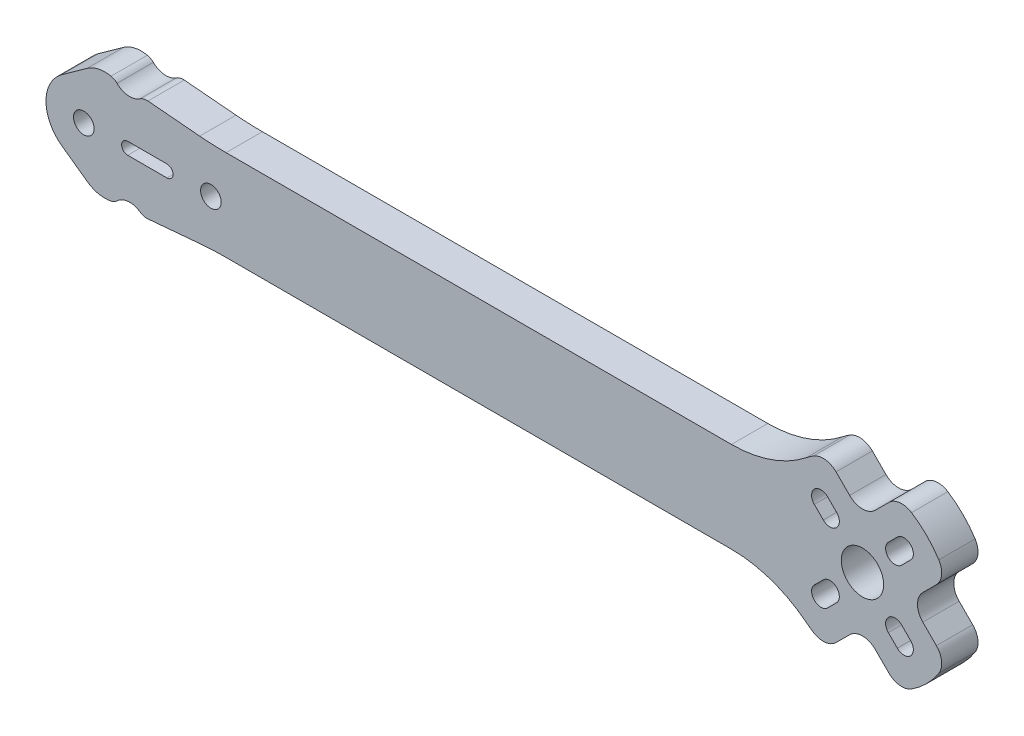
SolidWorks part; units mm, degrees
material "Thornel Mat VMA"
ref_plane "Front Plane" through (0, 0, 0) normal (0, 0, 1) x (1, 0, 0)
ref_plane "Top Plane" through (0, 0, 0) normal (0, 1, 0) x (1, 0, 0)
ref_plane "Right Plane" through (0, 0, 0) normal (1, 0, 0) x (0, 0, -1)
sketch "Sketch1" plane through (0, 0, 0) normal (0, 0, 1) x (1, 0, 0)
  line L0 (6.8589, 6.8589) -> (5.374, 5.374) construction
  line L2 (7.955, 5.7629) -> (6.47, 4.278)
  line L3 (5.7629, 7.955) -> (4.278, 6.47)
  line L4 (-6.8589, 6.8589) -> (-5.374, 5.374) construction
  line L5 (-5.7629, 7.955) -> (-4.278, 6.47)
  line L6 (-7.955, 5.7629) -> (-6.47, 4.278)
  line L7 (5.374, -5.374) -> (-5.374, 5.374) construction
  line L8 (6.8589, -6.8589) -> (5.374, -5.374) construction
  line L9 (5.7629, -7.955) -> (4.278, -6.47)
  line L11 (7.955, -5.7629) -> (6.47, -4.278)
  line L12 (-6.8589, -6.8589) -> (-5.374, -5.374) construction
  line L13 (-7.955, -5.7629) -> (-6.47, -4.278)
  line L14 (-5.7629, -7.955) -> (-4.278, -6.47)
  line L15 (-118.078, -8.4386) -> (-109.5245, -7.6903)
  line L16 (-105.1667, -7.5) -> (-21.6506, -7.5)
  line L17 (-4.367, -12.2159) -> (-2.1213, -9.9702)
  line L18 (2.1213, -9.9702) -> (4.367, -12.2159)
  line L19 (12.2159, -4.367) -> (9.9702, -2.1213)
  line L20 (9.9702, 2.1213) -> (12.2159, 4.367)
  line L21 (4.367, 12.2159) -> (2.1213, 9.9702)
  line L22 (-2.1213, 9.9702) -> (-4.367, 12.2159)
  line L23 (-21.6506, 7.5) -> (-105.1667, 7.5)
  line L24 (-109.5245, 7.6903) -> (-118.078, 8.4386)
  line L25 (-128.1078, 8.1033) -> (-132.3227, 5.0768)
  line L26 (-132.3227, -5.0768) -> (-128.1078, -8.1033)
  line L27 (-121.4272, 1) -> (-114.9272, 1)
  line L28 (-114.9272, -1) -> (-121.4272, -1)
  line L29 (0, 0) -> (-2.4749, 0) construction
  line L30 (-2.4749, 0) -> (-2.4749, 2.4749) construction
  circle A1 centre (0, 0) radius 3.5
  arc A20 (-124.1818, -8.9388) -> (-123.1893, -8.4119) centre (-124.5857, -6.98) ccw
  arc A21 (-119.3893, -8.0916) -> (-123.1893, -8.4119) centre (-121.0948, -10.5597) ccw
  arc A22 (-119.3893, -8.0916) -> (-118.078, -8.4386) centre (-118.2523, -6.4462) ccw
  arc A23 (-105.1667, -7.5) -> (-109.5245, -7.6903) centre (-105.1667, -57.5) ccw
  arc A24 (-9.2788, -11.7857) -> (-21.6506, -7.5) centre (-21.6506, -27.5) ccw
  arc A25 (-9.2788, -11.7857) -> (-8.1105, -12.6183) centre (0, 0) ccw
  arc A26 (-8.1105, -12.6183) -> (-4.367, -12.2159) centre (-6.4884, -10.0946) ccw
  arc A27 (2.1213, -9.9702) -> (-2.1213, -9.9702) centre (0, -12.0915) ccw
  arc A28 (4.367, -12.2159) -> (8.1105, -12.6183) centre (6.4884, -10.0946) ccw
  arc A29 (8.1105, -12.6183) -> (12.6183, -8.1105) centre (0, 0) ccw
  arc A30 (12.6183, -8.1105) -> (12.2159, -4.367) centre (10.0946, -6.4884) ccw
  arc A31 (9.9702, 2.1213) -> (9.9702, -2.1213) centre (12.0915, 0) ccw
  arc A32 (12.2159, 4.367) -> (12.6183, 8.1105) centre (10.0946, 6.4884) ccw
  arc A33 (12.6183, 8.1105) -> (8.1105, 12.6183) centre (0, 0) ccw
  arc A34 (8.1105, 12.6183) -> (4.367, 12.2159) centre (6.4884, 10.0946) ccw
  arc A35 (-2.1213, 9.9702) -> (2.1213, 9.9702) centre (0, 12.0915) ccw
  arc A36 (-4.367, 12.2159) -> (-8.1105, 12.6183) centre (-6.4884, 10.0946) ccw
  arc A37 (-8.1105, 12.6183) -> (-9.2788, 11.7857) centre (0, 0) ccw
  arc A38 (-21.6506, 7.5) -> (-9.2788, 11.7857) centre (-21.6506, 27.5) ccw
  arc A39 (-109.5245, 7.6903) -> (-105.1667, 7.5) centre (-105.1667, 57.5) ccw
  arc A40 (-118.078, 8.4386) -> (-119.3893, 8.0916) centre (-118.2523, 6.4462) ccw
  arc A41 (-123.1893, 8.4119) -> (-119.3893, 8.0916) centre (-121.0948, 10.5597) ccw
  arc A42 (-123.1893, 8.4119) -> (-124.1818, 8.9388) centre (-124.5857, 6.98) ccw
  arc A43 (-124.1818, 8.9388) -> (-128.1078, 8.1033) centre (-125.1915, 4.0418) ccw
  arc A44 (-132.3227, 5.0768) -> (-132.3227, -5.0768) centre (-128.6772, 0) ccw
  arc A45 (-128.1078, -8.1033) -> (-124.1818, -8.9388) centre (-125.1915, -4.0418) ccw
  arc A46 (-121.4272, 1) -> (-121.4272, -1) centre (-121.4272, 0) ccw
  arc A47 (-114.9272, -1) -> (-114.9272, 1) centre (-114.9272, 0) ccw
  arc A48 (-5.7629, 7.955) -> (-7.955, 5.7629) centre (-6.8589, 6.8589) ccw
  arc A49 (-6.47, 4.278) -> (-4.278, 6.47) centre (-5.374, 5.374) ccw
  arc A50 (7.955, 5.7629) -> (5.7629, 7.955) centre (6.8589, 6.8589) ccw
  arc A51 (4.278, 6.47) -> (6.47, 4.278) centre (5.374, 5.374) ccw
  arc A52 (5.7629, -7.955) -> (7.955, -5.7629) centre (6.8589, -6.8589) ccw
  arc A53 (6.47, -4.278) -> (4.278, -6.47) centre (5.374, -5.374) ccw
  arc A54 (-7.955, -5.7629) -> (-5.7629, -7.955) centre (-6.8589, -6.8589) ccw
  arc A55 (-4.278, -6.47) -> (-6.47, -4.278) centre (-5.374, -5.374) ccw
  point P12 (6.1165, 6.1165)
  point P21 (-6.1165, 6.1165)
  point P26 (6.1165, -6.1165)
  point P29 (0, 0)
  point P102 (-6.1165, -6.1165)
  point P107 (0, 0)
  dimension "D1" = 7
  dimension "D2" = 3.1
  dimension "D3" = 2.1
  dimension "D4" = 15.2
  dimension "D5" = 4
extrude "Boss-Extrude1" add sketch "Sketch1" along normal blind 6
hole_wizard "M3 Clearance Hole1" positions "Sketch2" profile "Sketch3" hole size "M3" standard "ANSI Metric" end condition up to next
sketch "Sketch2" plane through (0, 0, 6) normal (0, 0, 1) x (1, 0, 0)
  line L0 (-128.6772, 0) -> (-107.6772, 0) construction
  arc A0 (-132.3227, 5.0768) -> (-132.3227, -5.0768) centre (-128.6772, 0) ccw construction
  point P0 (-107.6772, 0)
  point P3 (-128.6772, 0)
  dimension "D1" = 21
sketch "Sketch3" plane through (-107.6772, 0, 6) normal (1, 0, 0) x (0, -1, 0)
  line L0 (0, 0) -> (0, 6)
  line L1 (0, 6) -> (1.7, 6)
  line L2 (1.7, 6) -> (1.7, 0)
  line L5 (1.7, 0) -> (0, 0)
  line L11 (0, -6.35) -> (0, 107.95) construction
  dimension "Thru Hole Dia." = 3.4
  dimension "Thru Hole Depth" = 6
